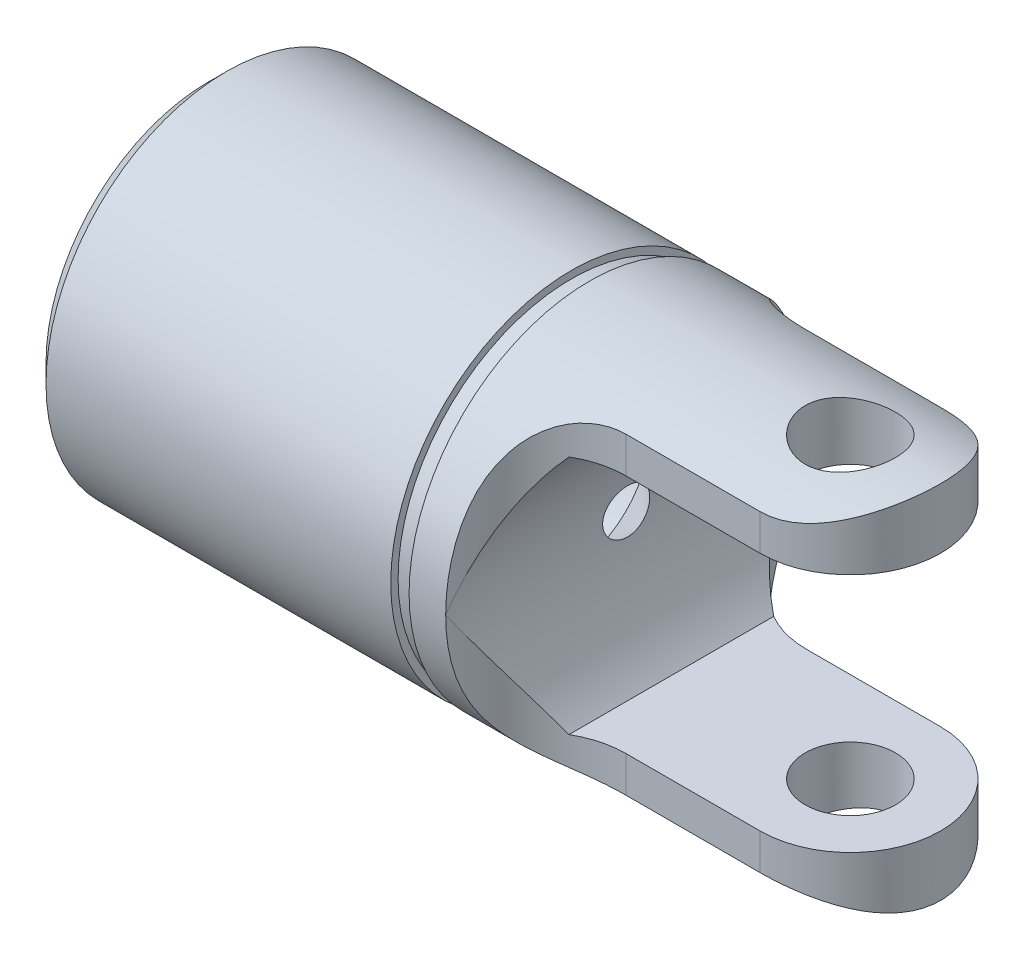
SolidWorks part; units mm, degrees
material "Zinc AC41A Alloy, As Cast"
ref_plane "Front Plane" through (0, 0, 0) normal (0, 0, 1) x (1, 0, 0)
ref_plane "Top Plane" through (0, 0, 0) normal (0, 1, 0) x (1, 0, 0)
ref_plane "Right Plane" through (0, 0, 0) normal (1, 0, 0) x (0, 0, -1)
sketch "Sketch0" plane through (0, 0, 0) normal (0, 1, 0) x (1, 0, 0)
  line L0 (-25.4, 0) -> (25.4, 0) construction
  line L1 (-25.4, 7.1437) -> (-25.4, -7.1437) construction
  line L2 (-11.1125, 3.175) -> (-11.1125, -3.175) construction
  line L3 (-11.1125, 3.175) -> (-7.9375, 0) construction
  line L4 (-7.9375, 0) -> (-11.1125, -3.175) construction
  line L5 (-9.525, 1.5875) -> (-9.525, -1.5875) construction
  point P7 (-11.1125, 0)
  point P8 (0, 0)
  point P12 (-9.525, 0)
sketch "Sketch1" plane through (0, 0, 0) normal (0, 1, 0) x (1, 0, 0)
  line L0 (-25.4, 7.1437) -> (-11.043, 7.1437)
  line L1 (3.5719, 7.1438) -> (3.5719, 0)
  line L2 (3.5719, 0) -> (-25.4, 0)
  line L3 (-25.4, 0) -> (-25.4, 7.1437)
  line L4 (-25.4, 7.1437) -> (-25.4, -7.1437) construction
  line L5 (-25.4, 0) -> (25.4, 0) construction
  line L6 (-10.3187, 7.1437) -> (3.5719, 7.1438)
  line L7 (-10.3187, 1.5875) -> (-10.3187, 6.854) construction
  line L8 (-11.043, 7.1437) -> (-11.043, 6.854)
  line L9 (-11.043, 6.854) -> (-10.3187, 6.854)
  line L10 (-10.3187, 7.1437) -> (-10.3187, 6.854)
  line L11 (0, 0) -> (7.1437, 0) construction
  line L12 (-9.525, 1.5875) -> (-11.1125, 1.5875) construction
  line L13 (-11.1125, 3.175) -> (-11.1125, -3.175) construction
  circle A0 centre (0, 0) radius 7.1437 construction
  dimension "D1" = 0.7243
  dimension "D2" = 0.2897
  dimension "D3" = 28.9719
revolve "Revolve1" add sketch "Sketch1" angle 360 about L0
chamfer "Chamfer1" distance 0.7144 angle 45 1 edges at (-25.4, 0, 7.1437)
sketch "Sketch2" plane through (0, 0, 0) normal (0, 1, 0) x (1, 0, 0)
  line L0 (-10.3187, 7.1437) -> (-8.8702, 7.1437) construction
  line L1 (-10.3187, 7.1437) -> (3.5719, 7.1438) construction
  line L2 (3.5719, 7.1437) -> (-10.3187, 7.1437) construction
  line L4 (-25.4, 0) -> (3.5719, 0) construction
  line L5 (-8.8702, 7.1437) -> (7.1437, 7.1437)
  line L6 (7.1437, 7.1437) -> (7.1437, -7.1437)
  line L7 (7.1437, -7.1437) -> (-8.8702, -7.1437)
  line L8 (0, 3.5719) -> (0, 0) construction
  line L9 (0, 3.5719) -> (-5.2983, 3.5719)
  line L10 (-8.8702, 7.1437) -> (-8.8702, -7.1437) construction
  line L11 (0, -3.5719) -> (-5.2983, -3.5719)
  arc A0 (-8.8702, 7.1437) -> (-5.2983, 3.5719) centre (-5.2983, 7.1437) ccw
  arc A1 (0, -3.5719) -> (0, 3.5719) centre (0, 0) ccw
  arc A2 (-5.2983, -3.5719) -> (-8.8702, -7.1437) centre (-5.2983, -7.1437) ccw
  dimension "D1" = 7.1437
  dimension "D2" = 1.4486
extrude "Extrude1" cut sketch "Sketch2" against normal through all and the other way through all
sketch "Sketch3" plane through (0, 0, 0) normal (0, 0, 1) x (1, 0, 0)
  line L0 (-7.0842, 4.7577) -> (-8.8702, 2.9718) construction
  line L1 (-7.0842, 4.7577) -> (7.1437, 4.7577)
  line L2 (-8.8702, 2.9718) -> (-8.8702, -2.9718) construction
  line L3 (-7.0842, -4.7577) -> (7.1437, -4.7577)
  line L4 (7.1437, 4.7577) -> (7.1437, -4.7577)
  line L5 (-8.8702, -2.9718) -> (-7.0842, -4.7577) construction
  line L6 (-8.8702, 0) -> (-5.2983, 0) construction
  line L7 (-5.2983, -6.1867) -> (-5.2983, 6.1867) construction
  line L8 (7.1437, 0) -> (-8.8702, 0) construction
  line L9 (-7.0842, 0) -> (-7.0842, 4.7577) construction
  arc A0 (-7.0842, 4.7577) -> (-7.0842, -4.7577) centre (-1.6399, 0) ccw
  dimension "D1" = 9.5155
extrude "Extrude3" cut sketch "Sketch3" against normal through all and the other way through all
sketch "Sketch4" plane through (-25.4, 0, 0) normal (-1, 0, 0) x (0, 0, 1)
  circle A0 centre (0, 0) radius 3.175
extrude "Extrude4" cut sketch "Sketch4" against normal up to vertex (14.2875 mm away) up to point (-11.1125, 0, -3.175)
sketch "Sketch5" plane through (-11.1125, 0, 0) normal (-1, 0, 0) x (0, 0, 1)
  circle A0 centre (0, 0) radius 3.175 construction
  circle A1 centre (0, 0) radius 3.175
extrude "Extrude5" cut sketch "Sketch5" against normal through all draft 45
sketch "Sketch6" plane through (0, 0, 0) normal (0, 1, 0) x (1, 0, 0)
  line L0 (-25.4, 0) -> (25.4, 0) construction
  line L1 (3.5719, 0) -> (1.7859, 0) construction
  line L2 (1.7859, 0) -> (0, 0) construction
  circle A0 centre (0, 0) radius 1.7859
  arc A1 (0, -3.5719) -> (0, 3.5719) centre (0, 0) ccw construction
  dimension "D1" = 3.5719
extrude "Extrude6" cut sketch "Sketch6" against normal through all and the other way through all
sketch "Sketch10" plane through (0, 0, 0) normal (0, 0, 1) x (1, 0, 0)
  line L0 (-7.0842, 4.7577) -> (7.0842, -4.7577) construction
  line L1 (-7.0842, 4.7577) -> (7.0842, 4.7577)
  line L2 (-7.0842, 4.7577) -> (-7.0842, -4.7577)
  line L3 (-7.0842, -4.7577) -> (7.0842, -4.7577)
  line L4 (7.0842, 4.7577) -> (7.0842, -4.7577)
  line L5 (0, 4.7577) -> (3.5719, 4.7577) construction
sketch "Sketch13" plane through (0, 0, 0) normal (0, 1, 0) x (1, 0, 0)
  circle A0 centre (0, 0) radius 1.7859 construction
  circle A1 centre (0, 0) radius 1.7859
sketch "Sketch14" plane through (0, 0, 0) normal (0, 1, 0) x (1, 0, 0)
  circle A1 centre (0, 0) radius 1.7859
  circle A2 centre (0, 0) radius 1.7859
  dimension "D1" = 0
sketch "Sketch15" plane through (-25.4, 0, 0) normal (-1, 0, 0) x (0, 0, 1)
  circle A0 centre (0, 0) radius 3.175 construction
  circle A1 centre (0, 0) radius 3.175
  circle A2 centre (0, 0) radius 6.35
  dimension "D1" = 3.175
equation "\"D2@Sketch3\" = \"D1@Sketch3\" / 4"
equation "\"D1@Extrude14\" = \"OD@Sketch0\""
equation "\"D1@Extrude16\" = \"D1@Extrude14\""
equation "\"D1@Sketch3\" = \"OD@Sketch0\"*.666"
equation "\"D1@Sketch1\" = \"D3@Sketch1\"*.025"
equation "\"D2@Sketch1\" = \"D1@Sketch1\"/2.5"
equation "\"D1@Chamfer1\" = \"OD@Sketch0\"/20"
equation "\"D1@Chamfer3\" = \"D1@Chamfer1\"*.50"
equation "\"D2@Sketch2\" = \"D1@Sketch1\"*2"
equation "\"D3@Sketch20\" = \"D2@Sketch20\"/12"
